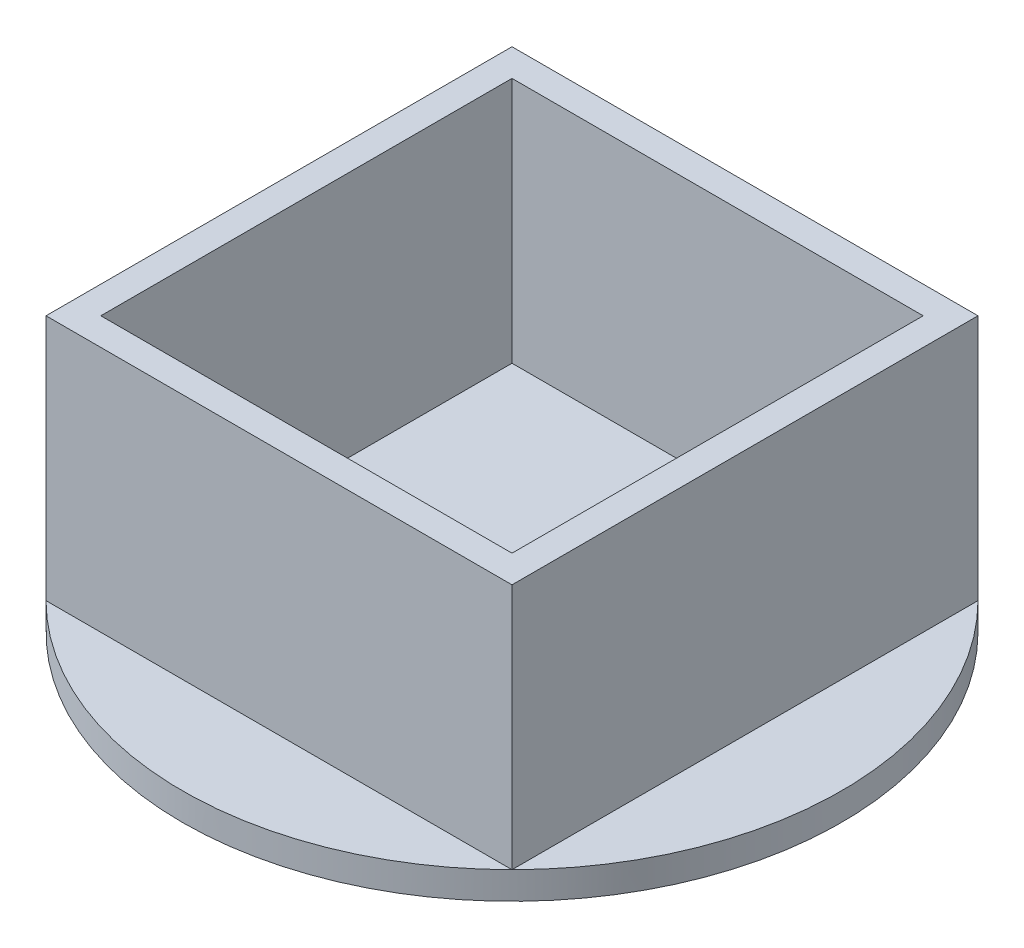
SolidWorks part; units mm, degrees
ref_plane "Front Plane" through (0, 0, 0) normal (0, 0, 1) x (1, 0, 0)
ref_plane "Top Plane" through (0, 0, 0) normal (0, 1, 0) x (1, 0, 0)
ref_plane "Right Plane" through (0, 0, 0) normal (1, 0, 0) x (0, 0, -1)
sketch "Sketch1" plane through (0, 0, 0) normal (0, 1, 0) x (1, 0, 0)
  line L1 (-7.5, 7.5) -> (7.5, 7.5)
  line L2 (-7.5, 7.5) -> (-7.5, -7.5)
  line L3 (-7.5, -7.5) -> (7.5, -7.5)
  line L4 (7.5, 7.5) -> (7.5, -7.5)
  line L5 (-7.5, 7.5) -> (7.5, -7.5) construction
  line L6 (-7.5, -7.5) -> (7.5, 7.5) construction
  point P0 (0, 0)
  dimension "D1" = 15
  dimension "D2" = 15
extrude "Extrude-Thin1" add sketch "Sketch1" along normal blind 10 thin thin type one direction wall 1
sketch "Sketch2" plane through (0, 0, 0) normal (0, 1, 0) x (1, 0, 0)
  circle A0 centre (0, 0) radius 12.0208
extrude "Boss-Extrude1" add sketch "Sketch2" along normal blind 1
